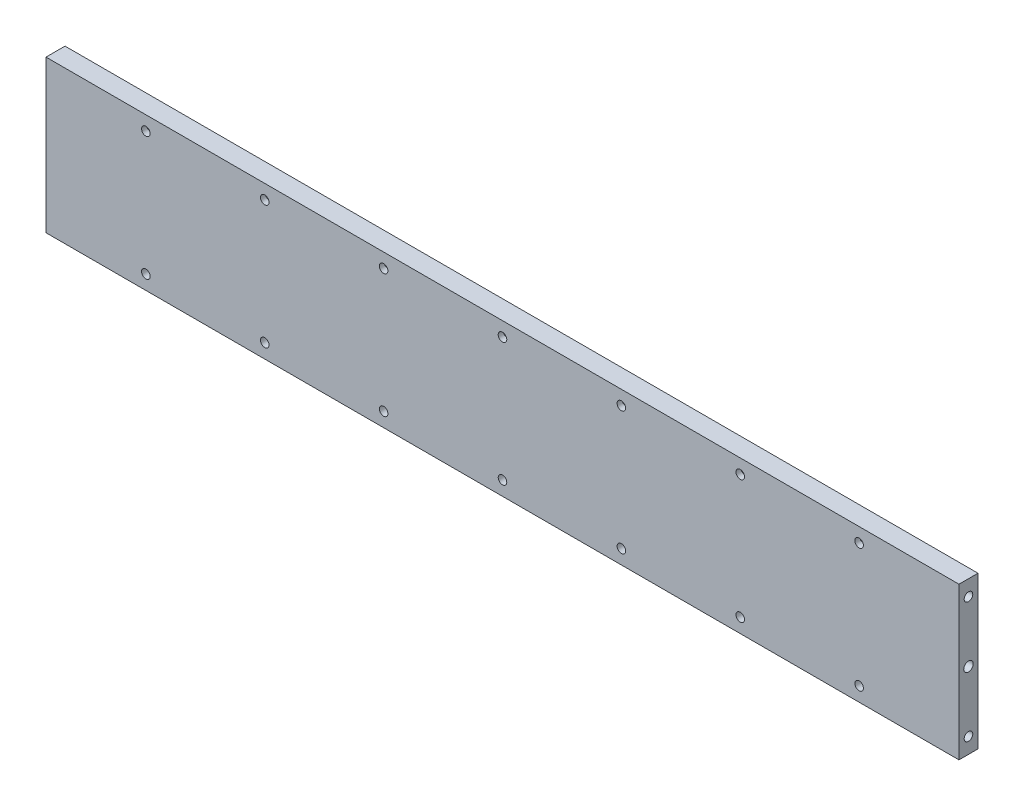
SolidWorks part; units mm, degrees
ref_plane "Front Plane" through (0, 0, 0) normal (0, 0, 1) x (1, 0, 0)
ref_plane "Top Plane" through (0, 0, 0) normal (0, 1, 0) x (1, 0, 0)
ref_plane "Right Plane" through (0, 0, 0) normal (1, 0, 0) x (0, 0, -1)
sketch "Sketch1" plane through (0, 0, 0) normal (0, 0, 1) x (1, 0, 0)
  line L0 (0, 26) -> (0, -26) construction
  line L1 (192, 32) -> (-192, 32)
  line L2 (192, 32) -> (192, -32)
  line L3 (192, -32) -> (-192, -32)
  line L4 (-192, 32) -> (-192, -32)
  line L5 (192, 32) -> (-192, -32) construction
  line L6 (192, -32) -> (-192, 32) construction
  point P0 (0, 0)
  point P8 (0, 0)
  circle B0 centre (0, 26) radius 1.8
  circle B1 centre (50, 26) radius 1.8
  circle B2 centre (100, 26) radius 1.8
  circle B3 centre (150, 26) radius 1.8
  circle B4 centre (-50, 26) radius 1.8
  circle B5 centre (-100, 26) radius 1.8
  circle B6 centre (-150, 26) radius 1.8
  circle B7 centre (-150, -26) radius 1.8
  circle B8 centre (-100, -26) radius 1.8
  circle B9 centre (-50, -26) radius 1.8
  circle B10 centre (150, -26) radius 1.8
  circle B11 centre (100, -26) radius 1.8
  circle B12 centre (50, -26) radius 1.8
  circle B13 centre (0, -26) radius 1.8
  dimension "D1" = 384
  dimension "D2" = 64
sketch_block_instance "Block2-1"
sketch_block "Block2"
extrude "Boss-Extrude1" add sketch "Sketch1" along normal blind 8
sketch "Sketch2" plane through (-192, 0, 0) normal (-1, 0, 0) x (0, 0, 1)
  line L0 (0, 0) -> (8, 0) construction
  line L1 (8, 32) -> (8, -32) construction
  line L2 (4, 32) -> (4, -32) construction
  line L3 (8, 32) -> (0, 32) construction
  line L4 (8, -32) -> (0, -32) construction
  circle A0 centre (4, 25.445) radius 1.8
  circle A1 centre (4, -25.445) radius 1.8
  circle A2 centre (4, 0) radius 2
  dimension "D1" = 25.445
extrude "Cut-Extrude1" cut sketch "Sketch2" against normal up to next
